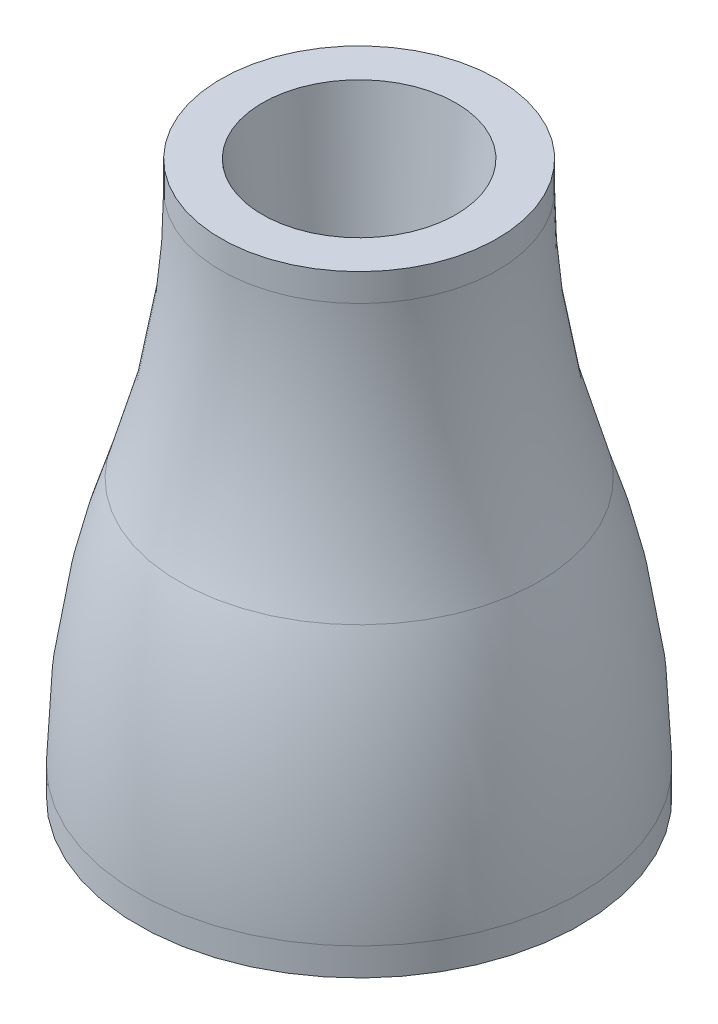
SolidWorks part; units mm, degrees
ref_plane "Front Plane" through (0, 0, 0) normal (0, 0, 1) x (1, 0, 0)
ref_plane "Top Plane" through (0, 0, 0) normal (0, 1, 0) x (1, 0, 0)
ref_plane "Right Plane" through (0, 0, 0) normal (1, 0, 0) x (0, 0, -1)
sketch "Sketch1" plane through (0, 0, 0) normal (0, 0, 1) x (1, 0, 0)
  line L0 (2.4, -2) -> (2.4, 0)
  line L1 (2.4, 0) -> (8, 0)
  line L2 (8, 0) -> (8, 1)
  line L5 (0.9, -2) -> (2.4, -2)
  line L6 (0, 0) -> (0, 20) construction
  line L7 (5, 19) -> (5, 20)
  line L8 (5, 20) -> (3.5, 20)
  line L9 (3.5, 20) -> (0.9, -2)
  arc A0 (8, 1) -> (6.5, 10) centre (-19.75, 1) ccw
  arc A1 (6.5, 10) -> (5, 19) centre (32.75, 19) cw
  point P9 (1.1636, -2)
  dimension "D1" = 2.4
  dimension "D2" = 1.5
  dimension "D3" = 2
  dimension "D4" = 8
  dimension "D5" = 1
  dimension "D6" = 20
  dimension "D7" = 1
  dimension "D8" = 5
  dimension "D9" = 1.5
revolve "Revolve1" add sketch "Sketch1" angle 360 about L6
